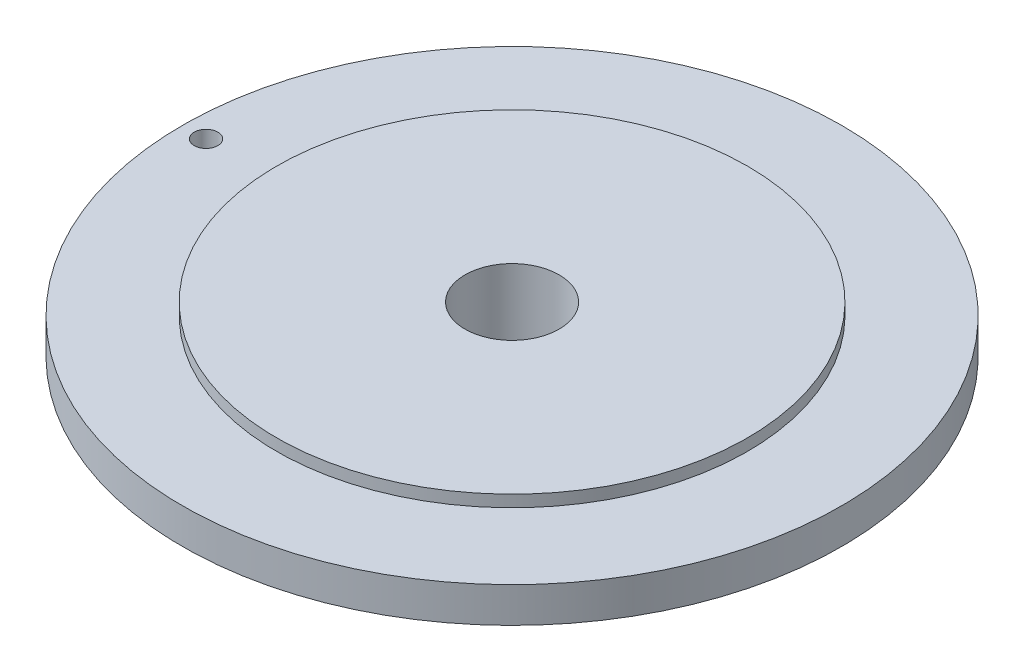
SolidWorks part; units mm, degrees
ref_plane "Front Plane" through (0, 0, 0) normal (0, 0, 1) x (1, 0, 0)
ref_plane "Top Plane" through (0, 0, 0) normal (0, 1, 0) x (1, 0, 0)
ref_plane "Right Plane" through (0, 0, 0) normal (1, 0, 0) x (0, 0, -1)
sketch "Sketch1" plane through (0, 0, 0) normal (0, 0, 1) x (1, 0, 0)
  line L0 (0, 0) -> (0, 12.5852) construction
  line L1 (-6.35, 0) -> (-6.35, 19.05)
  line L3 (-44.45, 17.4625) -> (-44.45, 12.7)
  line L4 (-44.45, 12.7) -> (-12.7, 12.7)
  line L5 (-12.7, 12.7) -> (-12.7, 0)
  line L7 (-10.9855, 0) -> (-12.7, 0)
  line L8 (-6.35, 19.05) -> (-31.75, 19.05)
  line L9 (-31.75, 19.05) -> (-31.75, 17.4625)
  line L10 (-31.75, 17.4625) -> (-44.45, 17.4625)
  line L11 (-10.9855, 0) -> (-10.9855, 2.032)
  line L12 (-10.9855, 2.032) -> (-7.9375, 2.032)
  line L13 (-7.9375, 2.032) -> (-7.9375, 0)
  line L14 (-7.9375, 0) -> (-6.35, 0)
  dimension "D1" = 6.35
  dimension "D2" = 12.7
  dimension "D3" = 44.45
  dimension "D4" = 12.7
  dimension "D5" = 12.7
  dimension "D6" = 6.35
  dimension "D7" = 1.5875
  dimension "D8" = 1.5875
  dimension "D9" = 3.048
  dimension "D10" = 2.032
revolve "Revolve1" add sketch "Sketch1" angle 360 about L0
hole_wizard "1/8 (0.125) Diameter Hole1" positions "Sketch2" profile "Sketch4" hole size "1/8" standard "ANSI Inch" end condition through all
sketch "Sketch2" plane through (0, 17.4625, 0) normal (0, 1, 0) x (1, 0, 0)
  point P0 (-41.275, 0)
  dimension "D1" = 41.275
sketch "Sketch4" plane through (-41.275, 17.4625, 0) normal (1, 0, 0) x (0, 0, 1)
  line L0 (0, 0) -> (0, 17.4625)
  line L1 (0, 17.4625) -> (1.5875, 17.4625)
  line L2 (1.5875, 17.4625) -> (1.5875, 0)
  line L5 (1.5875, 0) -> (0, 0)
  line L11 (0, -6.35) -> (0, 107.95) construction
  dimension "Thru Hole Dia." = 3.175
  dimension "Thru Hole Depth" = 17.4625
